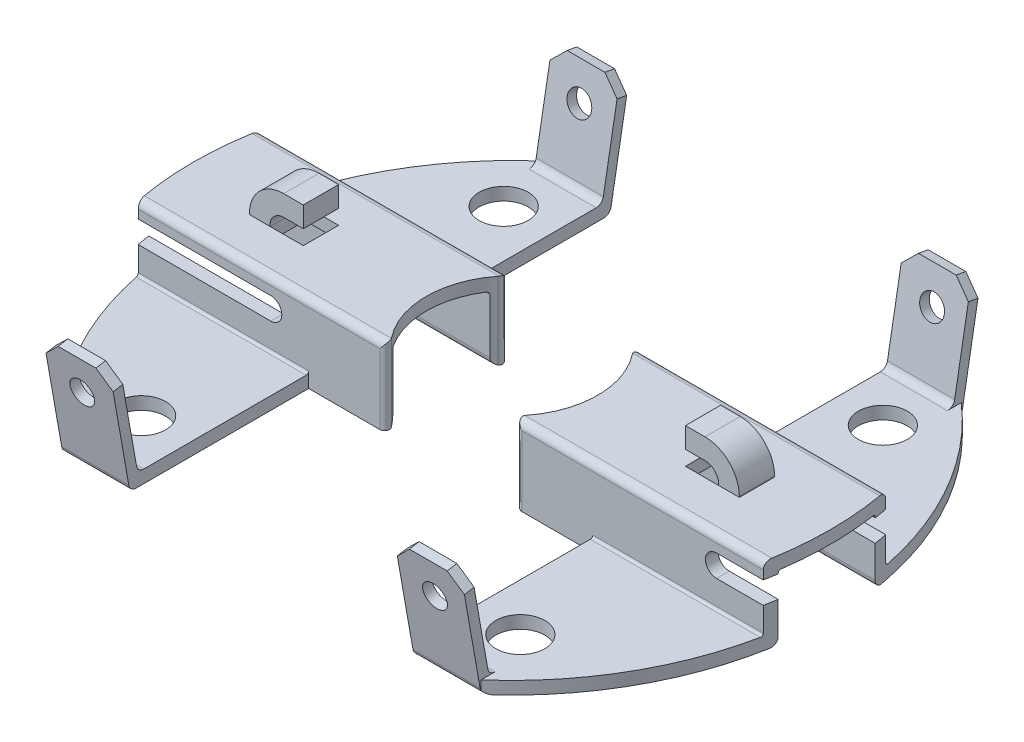
SolidWorks part; units mm, degrees
ref_plane "Front Plane" through (0, 0, 0) normal (0, 0, 1) x (1, 0, 0)
ref_plane "Top Plane" through (0, 0, 0) normal (0, 1, 0) x (1, 0, 0)
ref_plane "Right Plane" through (0, 0, 0) normal (1, 0, 0) x (0, 0, -1)
sketch "Sketch1" plane through (0, 0, 0) normal (0, 1, 0) x (1, 0, 0)
  line L0 (0, 0) -> (0, 23.3438) construction
  line L1 (0, 0) -> (-35.8468, 0) construction
  line L2 (-7.366, 12.446) -> (-7.366, 3.175)
  line L3 (-10.8479, 12.446) -> (-7.366, 12.446)
  line L4 (-10.8479, -12.446) -> (-7.366, -12.446)
  line L5 (10.8479, -12.446) -> (7.366, -12.446)
  line L6 (7.366, 12.446) -> (7.366, 3.175)
  line L7 (10.8479, 12.446) -> (7.366, 12.446)
  line L8 (-7.366, -3.175) -> (-3.6808, -3.175)
  line L9 (-7.366, 3.175) -> (-3.6808, 3.175)
  line L10 (7.366, -3.175) -> (3.6808, -3.175)
  line L11 (7.366, 3.175) -> (3.6808, 3.175)
  line L12 (-7.366, -3.175) -> (-7.366, -12.446)
  line L13 (7.366, -3.175) -> (7.366, -12.446)
  arc A0 (-10.8479, 12.446) -> (-10.8479, -12.446) centre (0, 0) ccw
  arc A1 (10.8479, -12.446) -> (10.8479, 12.446) centre (0, 0) ccw
  circle A2 centre (-9.8298, 9.398) radius 1.27
  circle A3 centre (-9.8298, -9.398) radius 1.27
  circle A4 centre (9.8298, -9.398) radius 1.27
  circle A5 centre (9.8298, 9.398) radius 1.27
  arc A6 (-3.4818, 2.7631) -> (-3.4818, -2.7631) centre (0, 0) ccw
  arc A7 (3.4818, 2.7631) -> (3.4818, -2.7631) centre (0, 0) cw
  arc A8 (3.6808, -3.175) -> (3.4818, -2.7631) centre (3.6808, -2.921) cw
  arc A9 (3.4818, 2.7631) -> (3.6808, 3.175) centre (3.6808, 2.921) cw
  arc A10 (-3.6808, -3.175) -> (-3.4818, -2.7631) centre (-3.6808, -2.921) ccw
  arc A11 (-3.4818, 2.7631) -> (-3.6808, 3.175) centre (-3.6808, 2.921) ccw
  point P11 (-5.08, 0)
  point P26 (-7.366, 3.175)
  point P34 (3.1109, -3.175)
  point P37 (3.1109, 3.175)
  point P40 (-3.1109, -3.175)
  point P43 (-3.1109, 3.175)
  dimension "D1" = 33.02
  dimension "D4" = 2.54
  dimension "D7" = 8.89
  dimension "D9" = 0.254
  dimension "D2" = 7.366
  dimension "D3" = 12.446
  dimension "D5" = 9.398
  dimension "D6" = 9.8298
  dimension "D8" = 6.35
extrude "Boss-Extrude1" add sketch "Sketch1" along normal blind 4.0132
sketch "Sketch2" plane through (0, 0, 0) normal (1, 0, 0) x (0, 0, -1)
  line L0 (0, 4.826) -> (0, -1.5824) construction
  line L1 (12.446, 4.0132) -> (12.446, 0.6604)
  line L2 (-3.175, 3.6322) -> (-3.175, 0.7874)
  line L3 (-3.302, 0.6604) -> (-12.446, 0.6604)
  line L4 (-12.446, 0) -> (12.446, 0)
  line L5 (12.446, 0) -> (12.446, 4.0132)
  line L6 (12.446, 4.0132) -> (-12.446, 4.0132)
  line L7 (-12.446, 4.0132) -> (-12.446, 0)
  line L8 (12.446, 4.0132) -> (-12.446, 4.0132) construction
  line L11 (-12.446, 4.0132) -> (-12.446, 0.6604)
  line L12 (3.175, 3.6322) -> (3.175, 0.7874)
  line L13 (3.302, 0.6604) -> (12.446, 0.6604)
  line L14 (-2.5146, 0.381) -> (-2.5146, 3.2258)
  line L15 (-2.794, 4.0132) -> (-12.446, 4.0132)
  line L16 (2.5146, 3.2258) -> (2.5146, 0.381)
  line L17 (12.446, 4.0132) -> (2.794, 4.0132)
  line L18 (-2.8956, 0) -> (2.8956, 0)
  line L19 (-2.3876, 3.3528) -> (2.3876, 3.3528)
  arc A0 (3.302, 0.6604) -> (3.175, 0.7874) centre (3.302, 0.7874) cw
  arc A1 (-3.175, 0.7874) -> (-3.302, 0.6604) centre (-3.302, 0.7874) cw
  arc A2 (2.5146, 0.381) -> (2.8956, 0) centre (2.8956, 0.381) ccw
  arc A3 (-2.5146, 0.381) -> (-2.8956, 0) centre (-2.8956, 0.381) cw
  arc A4 (3.175, 3.6322) -> (2.794, 4.0132) centre (2.794, 3.6322) ccw
  arc A5 (-2.794, 4.0132) -> (-3.175, 3.6322) centre (-2.794, 3.6322) ccw
  arc A6 (2.5146, 3.2258) -> (2.3876, 3.3528) centre (2.3876, 3.2258) ccw
  arc A7 (-2.3876, 3.3528) -> (-2.5146, 3.2258) centre (-2.3876, 3.2258) ccw
  point P8 (-3.175, 3.3528)
  point P14 (2.667, 3.3528)
  point P16 (12.446, 3.3528)
  point P19 (3.175, 0.6604)
  point P22 (-3.175, 0.6604)
  point P25 (2.5146, 0)
  point P33 (2.667, 4.0132)
  dimension "D7" = 0.127
  dimension "D8" = 0.381
  dimension "D3" = 0.381
  dimension "D5" = 0.127
  dimension "D4" = 0.6604
  dimension "D6" = 0.6604
  dimension "D1" = 0
extrude "Cut-Extrude1" cut sketch "Sketch2" against normal through all and the other way through all
sketch "Sketch4" plane through (0, 0, -3.175) normal (0, 0, -1) x (-1, 0, 0)
  line L1 (-16.3174, 3.2258) -> (-16.3174, 0.381) construction
  line L2 (-3.4608, 4.0132) -> (-16.2719, 4.0132) construction
  line L3 (-16.3174, 3.2258) -> (-16.3174, 0.381)
  line L4 (-16.7609, 2.6162) -> (-9.3324, 2.6162) construction
  line L5 (-16.7609, 3.1877) -> (-9.3324, 3.1877)
  line L6 (-16.7609, 2.0447) -> (-9.3324, 2.0447)
  line L7 (17.9767, 2.6162) -> (13.7774, 2.6162) construction
  line L8 (17.9767, 2.0447) -> (13.7774, 2.0447)
  line L9 (17.9767, 3.1877) -> (13.7774, 3.1877)
  line L11 (16.3174, 0.381) -> (16.3174, 3.2258) construction
  line L12 (16.2719, 4.0132) -> (3.4608, 4.0132) construction
  line L13 (16.3174, 0.381) -> (16.3174, 3.2258)
  line L14 (-3.4608, 4.0132) -> (-16.2719, 4.0132)
  line L15 (16.2719, 4.0132) -> (3.4608, 4.0132)
  arc A0 (-16.7609, 3.1877) -> (-16.7609, 2.0447) centre (-16.7609, 2.6162) ccw
  arc A1 (-9.3324, 2.0447) -> (-9.3324, 3.1877) centre (-9.3324, 2.6162) ccw
  arc A2 (17.9767, 2.0447) -> (17.9767, 3.1877) centre (17.9767, 2.6162) ccw
  arc A3 (13.7774, 3.1877) -> (13.7774, 2.0447) centre (13.7774, 2.6162) ccw
  point P6 (-13.0467, 2.6162)
  point P13 (15.877, 2.6162)
  dimension "D1" = 1.143
  dimension "D2" = 1.397
  dimension "D3" = 6.985
  dimension "D4" = 1.143
  dimension "D5" = 2.54
extrude "Cut-Extrude2" cut sketch "Sketch4" against normal blind 4.826 contours L5 A1 L6 A0 | L9 A3 L8 A2
sketch "Sketch5" plane through (0, 0, 3.175) normal (0, 0, 1) x (1, 0, 0)
  line L0 (-16.2719, 4.0132) -> (-3.4608, 4.0132) construction
  line L1 (3.4608, 4.0132) -> (16.2719, 4.0132) construction
  line L2 (-16.7609, 2.6162) -> (-9.3324, 2.6162) construction
  line L3 (-16.7609, 3.1877) -> (-9.3324, 3.1877)
  line L4 (-16.7609, 2.0447) -> (-9.3324, 2.0447)
  line L5 (17.9767, 2.6162) -> (13.7774, 2.6162) construction
  line L6 (17.9767, 2.0447) -> (13.7774, 2.0447)
  line L7 (17.9767, 3.1877) -> (13.7774, 3.1877)
  line L8 (-16.2719, 4.0132) -> (-3.4608, 4.0132)
  line L9 (3.4608, 4.0132) -> (16.2719, 4.0132)
  line L10 (-16.3174, 3.2258) -> (-16.3174, 0.381) construction
  line L13 (16.3174, 0.381) -> (16.3174, 3.2258) construction
  line L14 (-16.3174, 3.2258) -> (-16.3174, 0.381)
  line L17 (16.3174, 0.381) -> (16.3174, 3.2258)
  arc A0 (-16.7609, 3.1877) -> (-16.7609, 2.0447) centre (-16.7609, 2.6162) ccw
  arc A1 (-9.3324, 2.0447) -> (-9.3324, 3.1877) centre (-9.3324, 2.6162) ccw
  arc A2 (17.9767, 2.0447) -> (17.9767, 3.1877) centre (17.9767, 2.6162) ccw
  arc A3 (13.7774, 3.1877) -> (13.7774, 2.0447) centre (13.7774, 2.6162) ccw
  point P6 (-13.0467, 2.6162)
  point P13 (15.877, 2.6162)
  dimension "D1" = 1.397
  dimension "D2" = 6.985
  dimension "D3" = 1.143
  dimension "D4" = 2.54
extrude "Cut-Extrude3" cut sketch "Sketch5" against normal blind 4.826 contours L3 A1 L4 A0 | L7 A3 L6 A2
sketch "Sketch6" plane through (0, 4.0132, 0) normal (0, 1, 0) x (1, 0, 0)
  line L0 (0, 0) -> (0, 12.2755) construction
  line L1 (1.0288, 0) -> (-22.411, 0) construction
  line L2 (-12.7, 0.9144) -> (-12.7, -0.9144)
  line L3 (-12.7, 0.9144) -> (-9.906, 0.9144)
  line L4 (-9.906, 0.9144) -> (-9.906, -0.9144)
  line L5 (-12.7, -0.9144) -> (-9.906, -0.9144)
  line L6 (12.7, -0.9144) -> (9.906, -0.9144)
  line L7 (12.7, 0.9144) -> (9.906, 0.9144)
  line L8 (9.906, 0.9144) -> (9.906, -0.9144)
  line L9 (12.7, 0.9144) -> (12.7, -0.9144)
  arc A0 (-16.2719, 2.794) -> (-16.2719, -2.794) centre (0, 0) ccw construction
  point P1 (-16.51, 0)
  point P5 (-12.7, 0)
  point P12 (-9.906, 0)
  dimension "D1" = 3.81
  dimension "D2" = 0.9144
  dimension "D3" = 2.794
extrude "Boss-Extrude2" add sketch "Sketch6" along normal blind 1.8288
sketch "Sketch7" plane through (0, 0, 0) normal (0, 0, 1) x (1, 0, 0)
  line L0 (-12.7, 4.0132) -> (-9.906, 4.0132) construction
  line L1 (-9.906, 4.0132) -> (-9.906, 5.842) construction
  line L3 (-12.7, 5.842) -> (-12.7, 4.0132) construction
  line L4 (9.906, 4.0132) -> (12.7, 4.0132) construction
  line L5 (12.7, 4.0132) -> (12.7, 5.842) construction
  line L6 (12.7, 5.842) -> (9.906, 5.842) construction
  line L7 (9.906, 5.842) -> (9.906, 4.0132) construction
  line L8 (-11.6314, 4.0132) -> (-9.906, 4.0132)
  line L9 (-9.906, 4.0132) -> (-9.906, 4.7752)
  line L10 (-12.7, 4.064) -> (-12.7, 5.842)
  line L11 (-12.7, 4.064) -> (-12.7, 4.0132)
  line L12 (9.906, 4.0132) -> (11.6314, 4.0132)
  line L13 (12.7, 4.0132) -> (12.7, 5.842)
  line L14 (12.7, 5.842) -> (10.922, 5.842)
  line L15 (9.906, 4.7752) -> (9.906, 4.0132)
  line L16 (0, 0) -> (0, 14.9182) construction
  line L17 (-9.906, 4.7752) -> (-10.922, 4.7752)
  line L18 (-12.7, 5.842) -> (-10.922, 5.842)
  line L19 (11.6314, 4.0132) -> (9.906, 4.0132)
  line L20 (9.906, 4.7752) -> (10.922, 4.7752)
  line L21 (9.906, 4.0132) -> (9.906, 4.7752)
  line L22 (12.7, 5.842) -> (10.922, 5.842)
  line L23 (12.7, 4.064) -> (12.7, 5.842)
  line L24 (-12.7, 5.842) -> (-9.906, 5.842) construction
  arc A0 (-10.922, 5.842) -> (-12.7, 4.064) centre (-10.922, 4.064) ccw
  arc A1 (-10.922, 4.7752) -> (-11.6314, 4.0132) centre (-10.922, 4.064) ccw
  arc A2 (10.922, 4.7752) -> (11.6314, 4.0132) centre (10.922, 4.064) cw
  arc A3 (10.922, 5.842) -> (12.7, 4.064) centre (10.922, 4.064) cw
  dimension "D1" = 1.778
extrude "Cut-Extrude4" cut sketch "Sketch7" against normal blind 1.8288 and the other way blind 1.8288 contours A2 L20 L15 L12 | L14 A3 L13 | A0 L18 L10 | L17 A1 L8 L9
sketch "Sketch9" plane through (0, 4.0132, 0) normal (0, 1, 0) x (1, 0, 0)
  line L0 (-11.6314, -0.9144) -> (-11.6314, 0.9144) construction
  line L1 (-9.906, -0.9144) -> (-9.906, 0.9144) construction
  line L2 (-9.906, -0.9144) -> (-10.922, -0.9144) construction
  line L3 (-11.6332, -0.9144) -> (-10.922, -0.9144) construction
  line L4 (-10.922, 0.9144) -> (-11.6332, 0.9144) construction
  line L5 (-10.922, 0.9144) -> (-9.906, 0.9144) construction
  line L6 (-11.6314, -0.9144) -> (-11.6314, 0.9144)
  line L7 (-9.906, -0.9144) -> (-9.906, 0.9144)
  line L8 (-9.906, -0.9144) -> (-10.922, -0.9144)
  line L9 (-11.6332, -0.9144) -> (-10.922, -0.9144)
  line L10 (-10.922, 0.9144) -> (-11.6332, 0.9144)
  line L11 (-10.922, 0.9144) -> (-9.906, 0.9144)
  line L12 (0, 0) -> (0, -18.0945) construction
  line L13 (11.6332, -0.9144) -> (10.922, -0.9144)
  line L14 (9.906, -0.9144) -> (10.922, -0.9144)
  line L15 (10.922, 0.9144) -> (9.906, 0.9144)
  line L16 (10.922, 0.9144) -> (11.6332, 0.9144)
  line L17 (11.6314, -0.9144) -> (11.6314, 0.9144)
  line L18 (9.906, -0.9144) -> (9.906, 0.9144)
  line M1 (-11.6314, 0.9144) -> (-11.6314, -0.9144)
extrude "Cut-Extrude7" cut sketch "Sketch9" against normal through all contours L11 L10 L9 L8 L7 M1 | L18 L14 L13 L17 L16 L15
ref_plane "Plane1" through (7.62, 0, 0) normal (1, 0, 0) x (0, 0, -1)
sketch "Sketch10" plane through (7.62, 0, 0) normal (1, 0, 0) x (0, 0, -1)
  line L0 (-12.446, 0) -> (-13.4456, 5.669)
  line L2 (-13.4456, 5.669) -> (-12.9453, 5.7573)
  line L3 (-12.0197, 0.508) -> (-12.446, 0)
  line L4 (-12.0197, 0.508) -> (-12.9453, 5.7573)
  line L5 (-12.0197, 0.508) -> (-2.8956, 0.508) construction
  line L6 (-12.446, 0) -> (-2.8956, 0) construction
  line L7 (0, 0) -> (0, 10.1866) construction
  line L8 (12.0197, 0.508) -> (12.446, 0)
  line L9 (12.446, 0) -> (13.4456, 5.669)
  line L10 (13.4456, 5.669) -> (12.9453, 5.7573)
  line L11 (12.0197, 0.508) -> (12.9453, 5.7573)
  dimension "D2" = 0.508
extrude "Boss-Extrude3" add sketch "Sketch10" along normal up to vertex and the other way up to surface
sketch "Sketch11" plane through (0, 0, 0) normal (0, 1, 0) x (1, 0, 0)
  line L0 (0, 0) -> (0, -16.2217) construction
  line L1 (0, 0) -> (23.0855, 0) construction
ref_plane "Plane3" through (0, 0, 0) normal (1, 0, 0) x (0, 0, -1)
sketch "Sketch12" plane through (0, 0, 0) normal (1, 0, 0) x (0, 0, -1)
  line L0 (12.0466, 0.6604) -> (12.9453, 5.7573) construction
  line L1 (12.9453, 5.7573) -> (13.4456, 5.669) construction
  line L2 (13.4456, 5.669) -> (12.446, 0) construction
  line L3 (-12.9453, 5.7573) -> (-12.0466, 0.6604) construction
  line L4 (-13.4456, 5.669) -> (-12.9453, 5.7573) construction
  line L5 (-12.446, 0) -> (-13.4456, 5.669) construction
  line L6 (12.0466, 0.6604) -> (12.9453, 5.7573)
  line L7 (12.9453, 5.7573) -> (13.4456, 5.669)
  line L8 (13.4456, 5.669) -> (12.446, 0)
  line L9 (-12.9453, 5.7573) -> (-12.0466, 0.6604)
  line L10 (-13.4456, 5.669) -> (-12.9453, 5.7573)
  line L11 (-12.446, 0) -> (-13.4456, 5.669)
  line L12 (12.0466, 0.6604) -> (12.446, 0)
  line L13 (-12.0466, 0.6604) -> (-12.446, 0)
extrude "Boss-Extrude4" add sketch "Sketch12" against normal up to vertex (10.8479 mm away) from vertex at -7.366 starting at point (-7.366, 0.6604, -12.446)
chamfer "Chamfer1" distance 0.762 angle 45 4 edges at (10.8479, 5.7132, 13.1955) (7.366, 5.7132, 13.1955) (7.366, 5.7132, -13.1955) (10.8479, 5.7132, -13.1955)
chamfer "Chamfer2" distance 0.762 angle 45 4 edges at (-7.366, 5.7132, 13.1955) (-10.8479, 5.7132, 13.1955) (-10.8479, 5.7132, -13.1955) (-7.366, 5.7132, -13.1955)
fillet "Fillet1" radius 0.381 4 edges at (-9.107, 0.6604, -12.0466) (-9.107, 0.6604, 12.0466) (-9.107, 0, 12.446) (-9.107, 0, -12.446)
fillet "Fillet2" radius 0.381 4 edges at (9.107, 0.6604, 12.0466) (9.107, 0, 12.446) (9.107, 0.6604, -12.0466) (9.107, 0, -12.446)
sketch "Sketch13" plane through (0, -2.1284, -12.0707) normal (0, -0.1736, -0.9848) x (-1, 0, 0)
  line L0 (-7.366, 7.1557) -> (-7.366, 2.4809) construction
  line L2 (-10.0859, 7.9177) -> (-8.128, 7.9177) construction
  line L3 (0, 0) -> (0, 24.2555) construction
  circle A0 centre (-9.144, 6.1397) radius 0.635
  circle A1 centre (9.144, 6.1397) radius 0.635
  dimension "D1" = 1.27
  dimension "D2" = 1.778
  dimension "D3" = 1.778
sketch "Sketch14" plane through (0, 0, 0) normal (0, 1, 0) x (1, 0, 0)
  point P0 (0, 0)
extrude "Cut-Extrude8" cut sketch "Sketch13" against normal blind 3.175
sketch "Sketch15" plane through (0, -2.1284, 12.0707) normal (0, -0.1736, 0.9848) x (1, 0, 0)
  line L0 (-10.0859, 7.9177) -> (-8.128, 7.9177) construction
  line L1 (-7.366, 7.1557) -> (-7.366, 2.4809) construction
  line L2 (0, 0) -> (0, 13.9784) construction
  circle A0 centre (-9.144, 6.1397) radius 0.635
  circle A1 centre (9.144, 6.1397) radius 0.635
  dimension "D1" = 1.27
  dimension "D2" = 1.778
  dimension "D3" = 1.778
extrude "Cut-Extrude9" cut sketch "Sketch15" against normal blind 3.175
